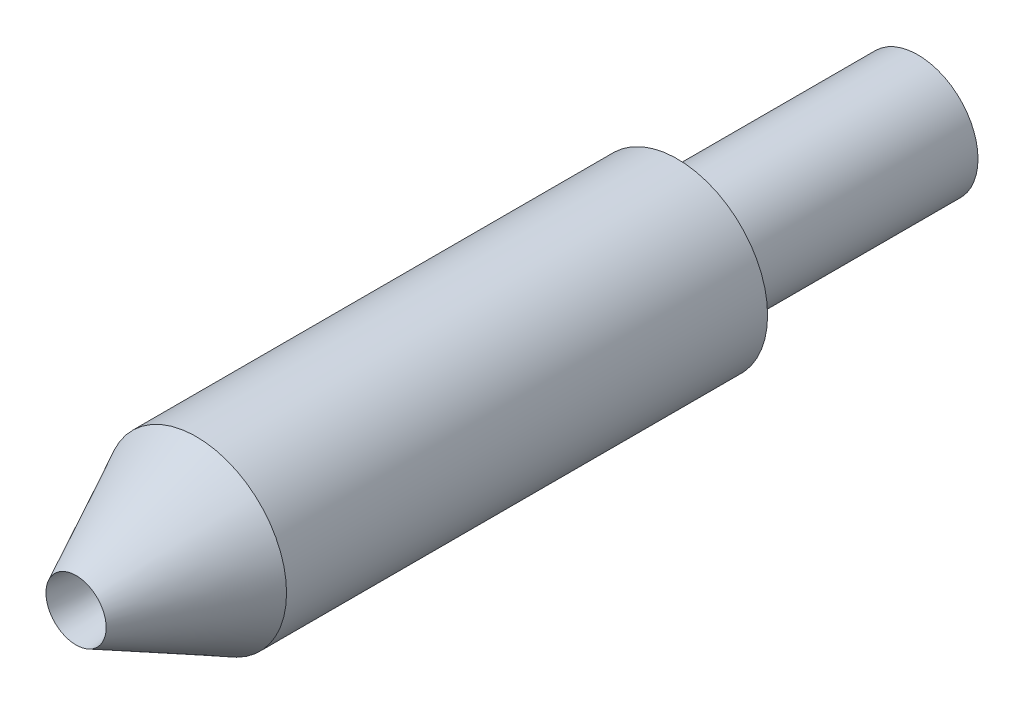
SolidWorks part; units mm, degrees
ref_plane "Front Plane" through (0, 0, 0) normal (0, 0, 1) x (1, 0, 0)
ref_plane "Top Plane" through (0, 0, 0) normal (0, 1, 0) x (1, 0, 0)
ref_plane "Right Plane" through (0, 0, 0) normal (1, 0, 0) x (0, 0, -1)
sketch "Sketch1" plane through (0, 0, 0) normal (0, 0, 1) x (1, 0, 0)
  circle A0 centre (0, 0) radius 1.1913
  dimension "D1" = 2.3825
extrude "Boss-Extrude1" add sketch "Sketch1" against normal blind 11.1125
sketch "Sketch2" plane through (0, 0, 0) normal (1, 0, 0) x (0, 0, -1)
  line L0 (0, 0.3975) -> (1.5875, 1.1913)
  line L1 (0, 1.1913) -> (0, -1.1913) construction
  line L2 (11.1125, 1.1913) -> (0, 1.1913) construction
  line L3 (1.5875, 1.1913) -> (0, 1.1913)
  line L4 (0, 1.1913) -> (0, 0.3975)
  line L5 (0, 0) -> (12.729, 0) construction
  dimension "D1" = 1.5875
  dimension "D2" = 0.7937
revolve "Cut-Revolve1" cut sketch "Sketch2" angle 360 about L5
sketch "Sketch4" plane through (0, 0, 0) normal (1, 0, 0) x (0, 0, -1)
  line L0 (0, 0.3975) -> (0, -0.3975) construction
  line L1 (11.1125, 1.1913) -> (7.9375, 1.1913)
  line L2 (11.1125, 1.1913) -> (11.1125, 0.7937)
  line L3 (11.1125, 0.7937) -> (7.9375, 0.7937)
  line L4 (7.9375, 1.1913) -> (7.9375, 0.7937)
  line L5 (1.5875, -1.1913) -> (11.1125, -1.1913) construction
  line L6 (0, 0) -> (14.7748, 0) construction
  dimension "D1" = 7.9375
  dimension "D2" = 1.985
revolve "Cut-Revolve2" cut sketch "Sketch4" angle 360 about L6
sketch "Sketch5" plane through (0, 0, 0) normal (1, 0, 0) x (0, 0, -1)
  line L0 (0, 0.3975) -> (1.5875, 0.1981)
  line L1 (1.5875, 1.1913) -> (1.5875, -1.1913) construction
  line L2 (1.5875, 0.1981) -> (1.5875, 0)
  line L3 (1.5875, 0) -> (0, 0)
  line L4 (0, 0) -> (0, 0.3975)
  line L5 (0, 0) -> (3.277, 0) construction
  dimension "D1" = 0.9931
revolve "Cut-Revolve3" cut sketch "Sketch5" angle 360 about L5
sketch "Sketch6" plane through (0, 0, 0) normal (0, 0, 1) x (1, 0, 0)
  circle A0 centre (0, 0) radius 0.3975
  dimension "D1" = 0.795
extrude "Cut-Extrude1" cut sketch "Sketch6" against normal blind 11.1125 from offset 2.3825 offset against normal yes
sketch "Sketch7" plane through (0, 0, 0) normal (1, 0, 0) x (0, 0, -1)
  line L0 (1.5875, 0.1981) -> (2.3825, 0.3975)
  line L1 (2.3825, 0.3975) -> (2.3825, 0)
  line L2 (2.3825, -0.3975) -> (2.3825, 0.3975) construction
  line L3 (2.3825, 0) -> (1.5875, 0)
  line L4 (1.5875, 1.1913) -> (1.5875, -1.1913) construction
  line L5 (1.5875, 0) -> (1.5875, 0.1981)
  line L6 (0, 0) -> (4.5416, 0) construction
revolve "Cut-Revolve4" cut sketch "Sketch7" angle 360 about L6
